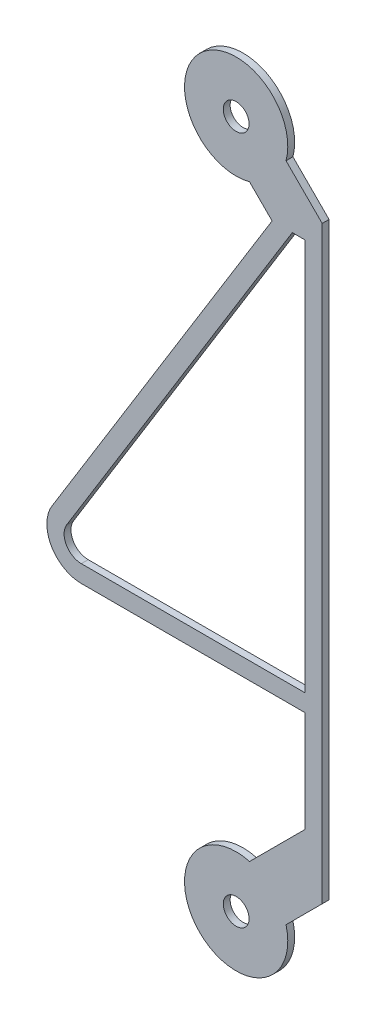
SolidWorks part; units mm, degrees
material "3.0517 (EN-AW 3003)"
ref_plane "Front Plane" through (0, 0, 0) normal (0, 0, 1) x (1, 0, 0)
ref_plane "Top Plane" through (0, 0, 0) normal (0, 1, 0) x (1, 0, 0)
ref_plane "Right Plane" through (0, 0, 0) normal (1, 0, 0) x (0, 0, -1)
sketch "Sketch1" plane through (0, 0, 0) normal (0, 0, 1) x (1, 0, 0)
  line L0 (0, 10) -> (0, -10) construction
  line L1 (1.0441, 7.8952) -> (-5.3512, -2.4751)
  line L2 (-4.5, -4) -> (2, -4)
  line L3 (2, -4) -> (2, -6.9393)
  line L4 (2.5, -8.5607) -> (1.4489, -9.6118)
  line L5 (2.5, -8.5607) -> (2.5, 8.5607)
  line L6 (1.6315, 7.8952) -> (-4.9256, -2.7375)
  line L7 (-4.5, -3.5) -> (2, -3.5)
  line L8 (2, -3.5) -> (2, 7.8952)
  line L9 (-0.0936, 5.0979) -> (-5.3958, -3.5) construction
  line L10 (2.5, 8.5607) -> (1.4489, 9.6118)
  line L11 (1.0441, 7.8952) -> (0.3882, 8.5511)
  line L12 (-3.2374, 0) -> (2, 0) construction
  line L13 (2, -6.9393) -> (0.3882, -8.5511)
  line L14 (-0.5303, 9.4697) -> (0.5303, 10.5303) construction
  line L15 (-0.5191, 5.3603) -> (-6.2916, -4) construction
  line L16 (-5.3958, -3.5) -> (2, -3.5) construction
  line L17 (-6.2916, -4) -> (2, -4) construction
  line L18 (-5.5, -3) -> (-5.5, -9.9984) construction
  line L19 (2, 8.4927) -> (1.1979, 9.0972) construction
  line L20 (1.0441, 7.8952) -> (1.599, 8.795) construction
  line L21 (1.6315, 7.8952) -> (2, 7.8952)
  line L22 (0.5303, -10.5303) -> (-0.5303, -9.4697) construction
  arc A0 (1.4489, 9.6118) -> (0.3882, 8.5511) centre (0, 10) ccw
  circle A1 centre (0, 10) radius 0.375
  arc A2 (0.3882, -8.5511) -> (1.4489, -9.6118) centre (0, -10) ccw
  circle A3 centre (0, -10) radius 0.375
  arc A4 (-4.9256, -2.7375) -> (-4.5, -3.5) centre (-4.5, -3) ccw
  arc A5 (-5.3512, -2.4751) -> (-4.5, -4) centre (-4.5, -3) ccw
  dimension "D2" = 3
  dimension "D3" = 0.75
  dimension "D4" = 1.5
  dimension "D5" = 2
  dimension "D9" = 0.5
  dimension "D10" = 1
  dimension "D7" = 0.5
  dimension "D1" = 20
  dimension "D6" = 6
  dimension "D11" = 8
  dimension "D12" = 45
  dimension "D8" = 0.5
extrude "Boss-Extrude1" add sketch "Sketch1" along normal mid plane 0.2
sketch "Sketch2" plane through (0, 0, 0) normal (0, 0, 1) x (1, 0, 0)
  line L0 (0.0835, 8.5023) -> (1.4977, 9.9165)
  line L1 (1.4977, -9.9165) -> (0.0835, -8.5023)
  line L10 (1.75, -3.25) -> (1.75, 7.6111)
  line L11 (-4.5, -3.25) -> (1.75, -3.25)
  line L12 (1.75, 7.6111) -> (-4.7128, -2.8688)
  line L13 (1.75, -3.25) -> (1.75, 7.6111)
  line L14 (-4.5, -3.25) -> (1.75, -3.25)
  line L15 (1.75, 7.6111) -> (-4.7128, -2.8688)
  line L16 (1.75, -4.25) -> (1.75, -6.8358)
  line L17 (1.75, -6.8358) -> (0.3084, -8.2774)
  line L18 (1.7226, -9.6916) -> (2.75, -8.6642)
  line L19 (2.75, -8.6642) -> (2.75, 8.6642)
  line L20 (2.75, 8.6642) -> (1.7226, 9.6916)
  line L21 (0.3084, 8.2774) -> (0.7276, 7.8582)
  line L22 (0.7276, 7.8582) -> (-5.564, -2.3439)
  line L23 (-4.5, -4.25) -> (1.75, -4.25)
  line L24 (1.75, -4.25) -> (1.75, -6.8358)
  line L25 (1.75, -6.8358) -> (0.0835, -8.5023)
  line L26 (1.4977, -9.9165) -> (2.75, -8.6642)
  line L27 (2.75, -8.6642) -> (2.75, 8.6642)
  line L28 (2.75, 8.6642) -> (1.4977, 9.9165)
  line L29 (0.0835, 8.5023) -> (0.7276, 7.8582)
  line L30 (0.7276, 7.8582) -> (-5.564, -2.3439)
  line L31 (-4.5, -4.25) -> (1.75, -4.25)
  arc A0 (1.4489, 9.6118) -> (0.3882, 8.5511) centre (0, 10) ccw construction
  arc A1 (1.4489, 9.6118) -> (0.3882, 8.5511) centre (0, 10) ccw construction
  arc A2 (0.3882, -8.5511) -> (1.4489, -9.6118) centre (0, -10) ccw construction
  arc A3 (0.3882, -8.5511) -> (1.4489, -9.6118) centre (0, -10) ccw construction
  arc A6 (0.3084, -8.2774) -> (1.7226, -9.6916) centre (0, -10) ccw
  arc A7 (1.7226, 9.6916) -> (0.3084, 8.2774) centre (0, 10) ccw
  arc A8 (-5.564, -2.3439) -> (-4.5, -4.25) centre (-4.5, -3) ccw
  arc A9 (-4.7128, -2.8688) -> (-4.5, -3.25) centre (-4.5, -3) ccw
  arc A10 (-4.7128, -2.8688) -> (-4.5, -3.25) centre (-4.5, -3) ccw
  arc A11 (-5.564, -2.3439) -> (-4.5, -4.25) centre (-4.5, -3) ccw
  dimension "D2" = 0.25
  dimension "D1" = 0.25
extrude "Boss-Extrude2" [suppressed] add sketch "Sketch2" along normal mid plane 0.6
